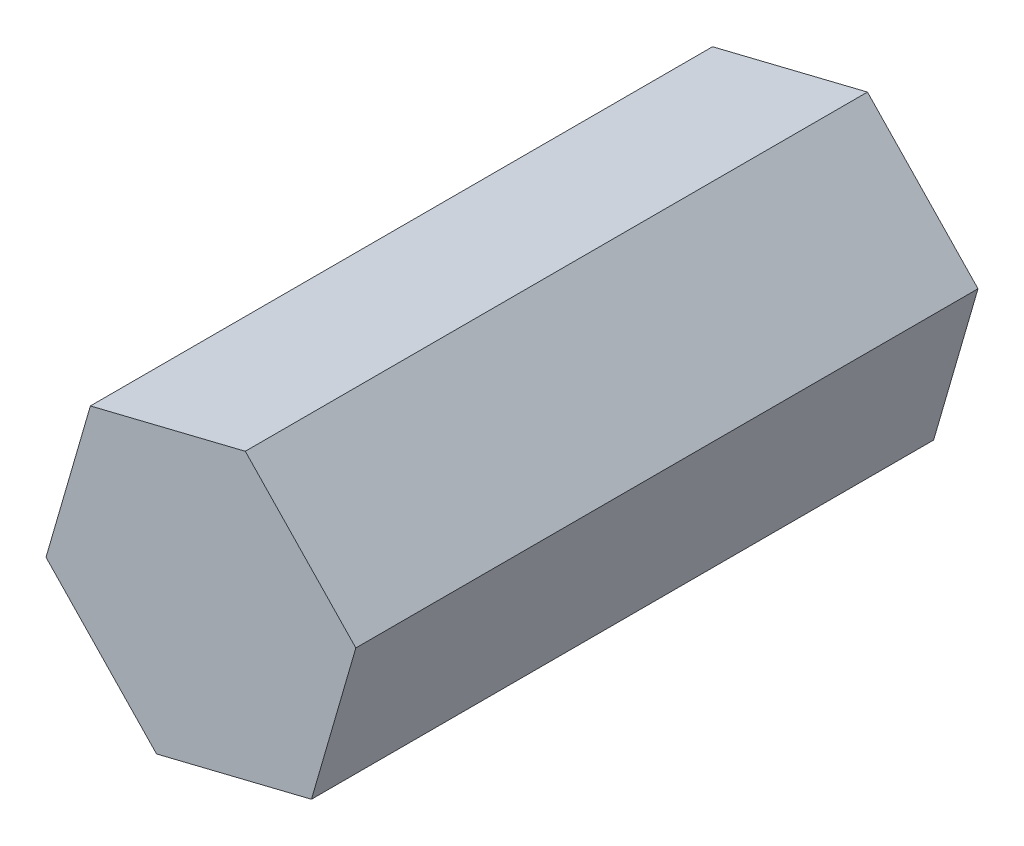
SolidWorks part; units mm, degrees
material "Brass"
ref_plane "Front Plane" through (0, 0, 0) normal (0, 0, 1) x (1, 0, 0)
ref_plane "Top Plane" through (0, 0, 0) normal (0, 1, 0) x (1, 0, 0)
ref_plane "Right Plane" through (0, 0, 0) normal (1, 0, 0) x (0, 0, -1)
sketch "Sketch1" plane through (0, 0, 0) normal (0, 0, 1) x (1, 0, 0)
  line L1 (-83.9851, 18.4648) -> (-87.72, 17.544)
  line L2 (-87.72, 17.544) -> (-88.7901, 13.849)
  line L3 (-88.7901, 13.849) -> (-86.1252, 11.0748)
  line L4 (-86.1252, 11.0748) -> (-82.3902, 11.9956)
  line L5 (-82.3902, 11.9956) -> (-81.3201, 15.6906)
  line L6 (-81.3201, 15.6906) -> (-83.9851, 18.4648)
  circle A0 centre (-85.0551, 14.7698) radius 3.3314 construction
extrude "Boss-Extrude1" add sketch "Sketch1" along normal blind 15
